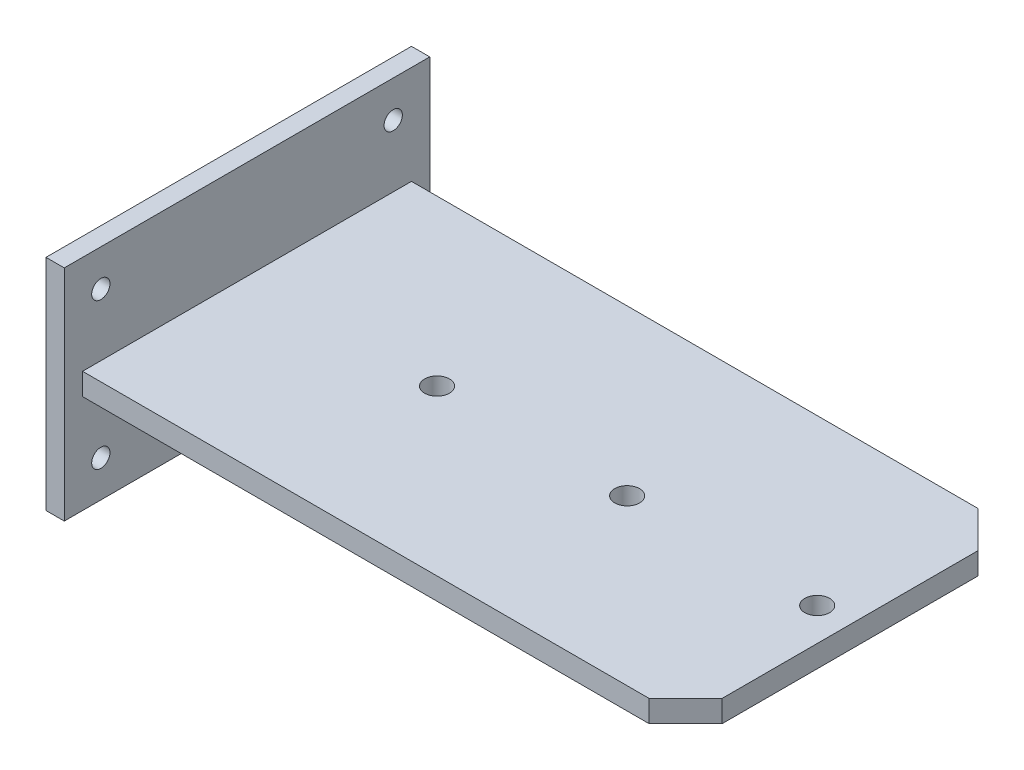
SolidWorks part; units mm, degrees
ref_plane "정면" through (0, 0, 0) normal (0, 0, 1) x (1, 0, 0)
ref_plane "평면" through (0, 0, 0) normal (0, 1, 0) x (1, 0, 0)
ref_plane "우측면" through (0, 0, 0) normal (1, 0, 0) x (0, 0, -1)
sketch "스케치1" plane through (0, 0, 0) normal (1, 0, 0) x (0, 0, -1)
  line L1 (-50, -30) -> (50, -30)
  line L2 (-50, -30) -> (-50, 30)
  line L3 (-50, 30) -> (50, 30)
  line L4 (50, -30) -> (50, 30)
  line L5 (0, 30) -> (0, -30) construction
  line L6 (-50, 0) -> (50, 0) construction
  point P0 (0, 0)
  dimension "D1" = 100
  dimension "D2" = 60
extrude "보스-돌출1" add sketch "스케치1" along normal blind 5
sketch "스케치2" plane through (5, 0, 0) normal (1, 0, 0) x (0, 0, -1)
  line L8 (40, -20) -> (40, 20)
  line L9 (40, 20) -> (-40, 20)
  line L10 (-40, 20) -> (-40, -20)
  line L11 (-40, -20) -> (40, -20)
  line L12 (40, -20) -> (40, 20) construction
  line L13 (40, 20) -> (-40, 20) construction
  line L14 (-40, 20) -> (-40, -20) construction
  line L15 (-40, -20) -> (40, -20) construction
  circle A0 centre (-40, 20) radius 2.5
  circle A1 centre (-40, -20) radius 2.5
  circle A2 centre (40, -20) radius 2.5
  circle A3 centre (40, 20) radius 2.5
  dimension "D2" = 5
  dimension "D1" = 10
extrude "컷-돌출1" cut sketch "스케치2" against normal up to next
sketch "스케치3" plane through (0, 0, 0) normal (0, 1, 0) x (1, 0, 0)
  line L0 (170, 35) -> (160, 45)
  line L3 (170, -35) -> (170, 35)
  line L4 (160, 45) -> (5, 45)
  line L5 (5, 45) -> (5, -45)
  line L6 (5, -45) -> (160, -45)
  line L7 (160, -45) -> (170, -35)
  dimension "D1" = 5
  dimension "D2" = 160
  dimension "D3" = 170
  dimension "D4" = 35
  dimension "D5" = 35
extrude "보스-돌출2" add sketch "스케치3" along normal mid plane 6
sketch "스케치4" plane through (0, 3, 0) normal (0, 1, 0) x (1, 0, 0)
  line L1 (109, -35) -> (109, 35) construction
  line L2 (161, -35) -> (161, 35)
  line L3 (161, -35) -> (161, 35) construction
  line L4 (57, -35) -> (57, 35) construction
  line L5 (161, 0) -> (57, 0) construction
  circle A0 centre (57, 0) radius 3.4
  circle A1 centre (109, 0) radius 3.4
  circle A2 centre (161, 0) radius 3.4
  dimension "D4" = 6.8
  dimension "D1" = 9
  dimension "D2" = 52
  dimension "D3" = 52
extrude "컷-돌출2" cut sketch "스케치4" against normal up to next
